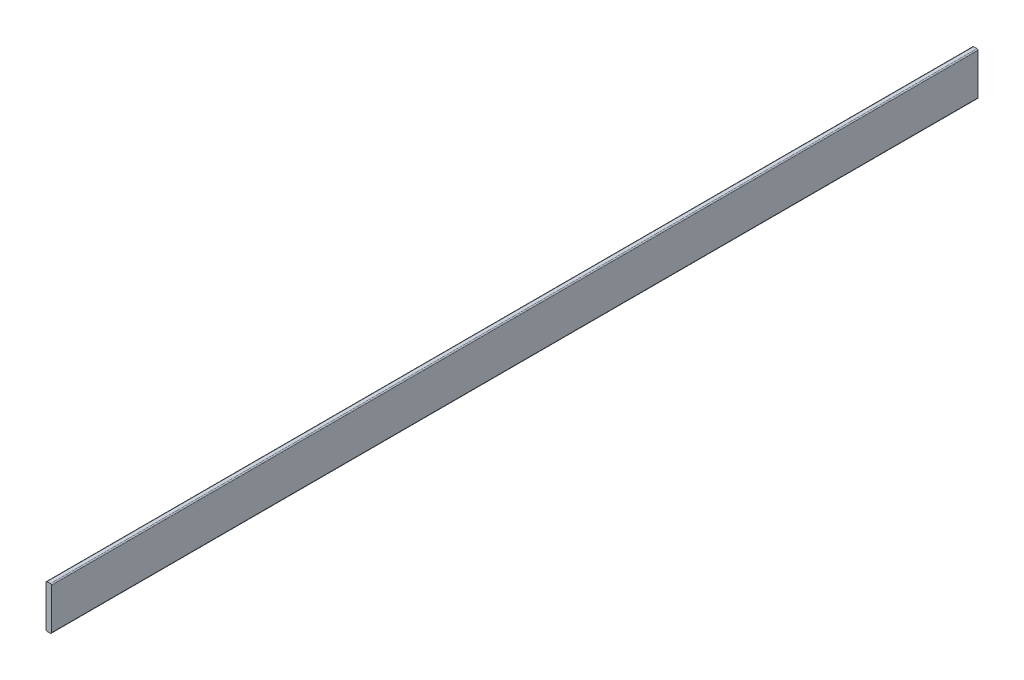
SolidWorks part; units mm, degrees
material "Plain Carbon Steel"
ref_plane "Front Plane" through (0, 0, 0) normal (0, 0, 1) x (1, 0, 0)
ref_plane "Top Plane" through (0, 0, 0) normal (0, 1, 0) x (1, 0, 0)
ref_plane "Right Plane" through (0, 0, 0) normal (1, 0, 0) x (0, 0, -1)
sketch "Sketch1" plane through (0, 0, 0) normal (0, 0, 1) x (1, 0, 0)
  line L1 (0.635, 0) -> (2.54, 0)
  line L2 (0, 0.635) -> (0, 24.765)
  line L3 (0.635, 25.4) -> (2.54, 25.4)
  line L4 (3.175, 0.635) -> (3.175, 24.765)
  arc A0 (2.54, 0) -> (3.175, 0.635) centre (2.54, 0.635) ccw
  arc A1 (0.635, 0) -> (0, 0.635) centre (0.635, 0.635) cw
  arc A2 (2.54, 25.4) -> (3.175, 24.765) centre (2.54, 24.765) cw
  arc A3 (0, 24.765) -> (0.635, 25.4) centre (0.635, 24.765) cw
  point P9 (0, 0)
  point P12 (3.175, 25.4)
  point P15 (0, 25.4)
  dimension "D3" = 0.635
  dimension "D1" = 25.4
  dimension "D2" = 3.175
extrude "Boss-Extrude1" add sketch "Sketch1" along normal blind 546.1
